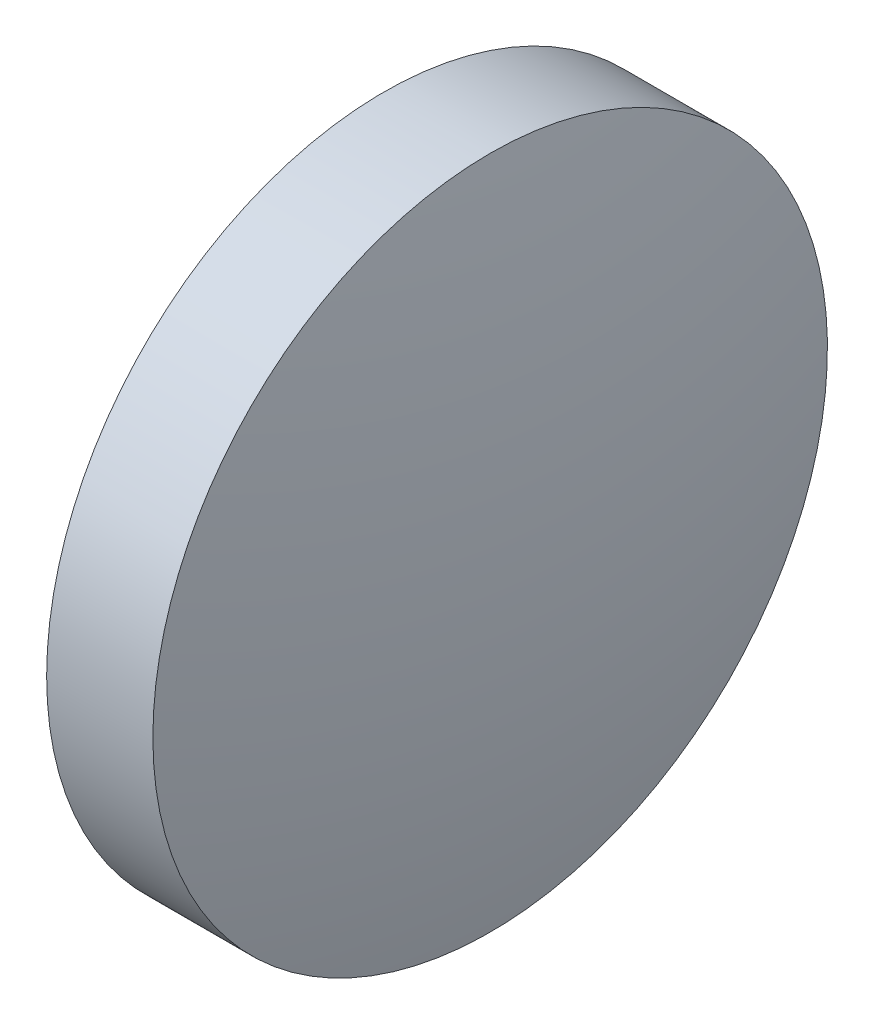
SolidWorks part; units mm, degrees
ref_plane "前视基准面" through (0, 0, 0) normal (0, 0, 1) x (1, 0, 0)
ref_plane "上视基准面" through (0, 0, 0) normal (0, 1, 0) x (1, 0, 0)
ref_plane "右视基准面" through (0, 0, 0) normal (1, 0, 0) x (0, 0, -1)
sketch "草图1" plane through (0, 0, 0) normal (0, 0, 1) x (1, 0, 0)
  line L0 (456.1344, 88.5342) -> (463.6528, 88.5342) construction
  line L1 (458.3949, 88.5342) -> (458.3949, 94.8842)
  line L2 (461.0949, 88.5342) -> (458.3949, 88.5342)
  line L5 (458.3949, 94.8842) -> (460.3949, 94.8842)
  arc A0 (461.0949, 88.5342) -> (460.3949, 94.8842) centre (431.9431, 88.5342) ccw
revolve "旋转1" add sketch "草图1" angle 360 about L0
